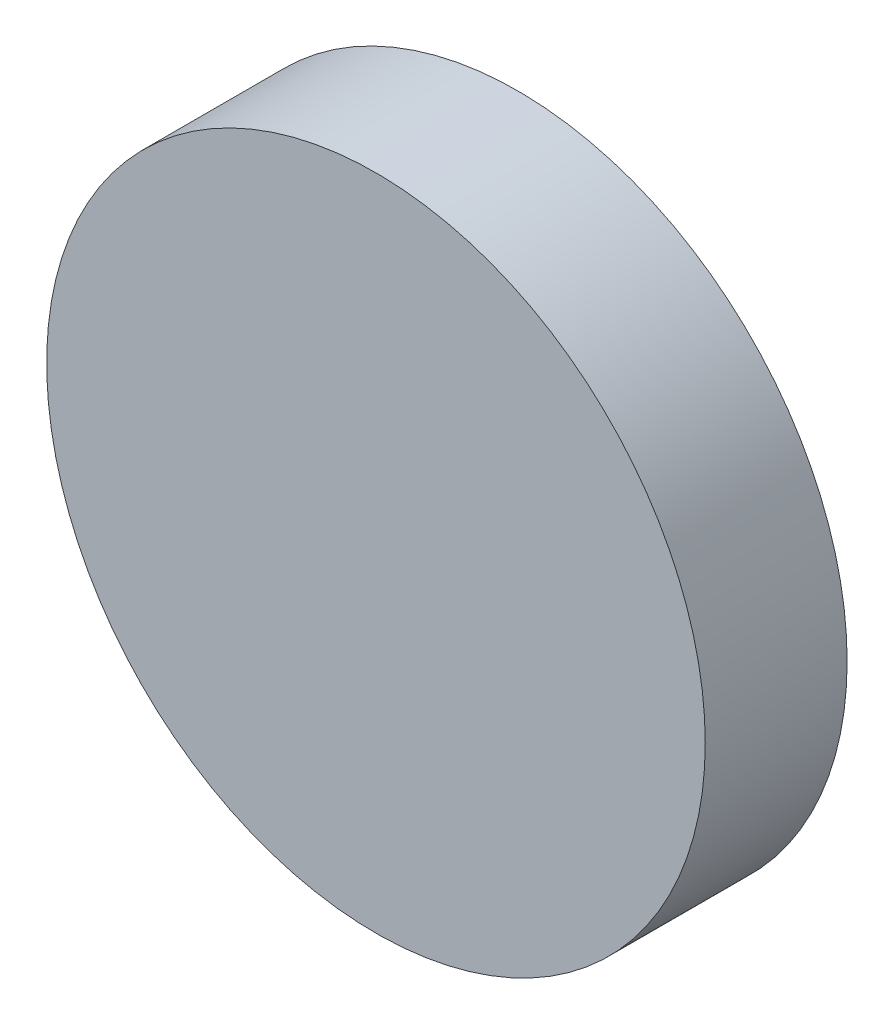
SolidWorks part; units mm, degrees
ref_plane "Plan de face" through (0, 0, 0) normal (0, 0, 1) x (1, 0, 0)
ref_plane "Plan de dessus" through (0, 0, 0) normal (0, 1, 0) x (1, 0, 0)
ref_plane "Plan de droite" through (0, 0, 0) normal (1, 0, 0) x (0, 0, -1)
sketch "Esquisse1" plane through (0, 0, 0) normal (0, 0, 1) x (1, 0, 0)
  circle A0 centre (0, 0) radius 13.925
extrude "Boss.-Extru.1" add sketch "Esquisse1" along normal blind 6
